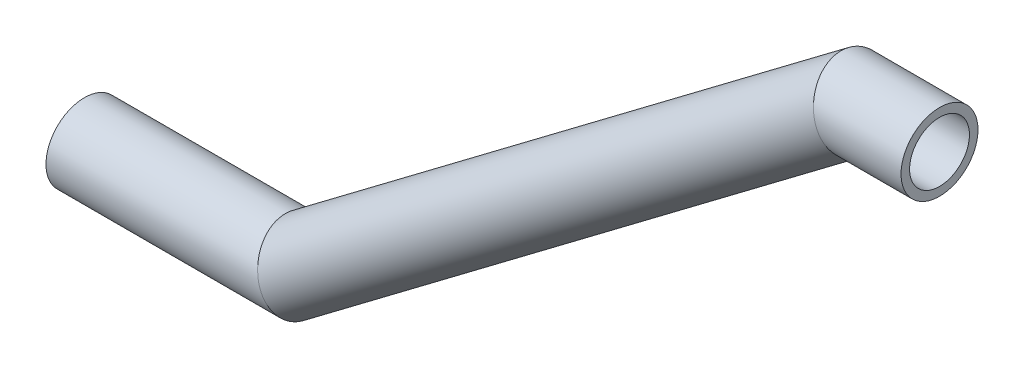
SolidWorks part; units mm, degrees
ref_plane "Front Plane" through (0, 0, 0) normal (0, 0, 1) x (1, 0, 0)
ref_plane "Top Plane" through (0, 0, 0) normal (0, 1, 0) x (1, 0, 0)
ref_plane "Right Plane" through (0, 0, 0) normal (1, 0, 0) x (0, 0, -1)
sketch "Sketch1" plane through (0, 0, 0) normal (0, 0, 1) x (1, 0, 0)
  line L0 (-25, 0) -> (0, 0)
  line L1 (0, 0) -> (65, 49)
  line L2 (65, 49) -> (75, 49)
  dimension "D1" = 65
  dimension "D2" = 49
  dimension "D3" = 10
  dimension "D4" = 25
sketch "Sketch2" plane through (0, 0, 0) normal (1, 0, 0) x (0, 0, -1)
  circle A0 centre (0, 0) radius 4.5
  circle A1 centre (0, 0) radius 3.5
  dimension "D1" = 9
  dimension "D2" = 7
sweep "Sweep1" add profiles "Sketch2" path "Sketch1"
